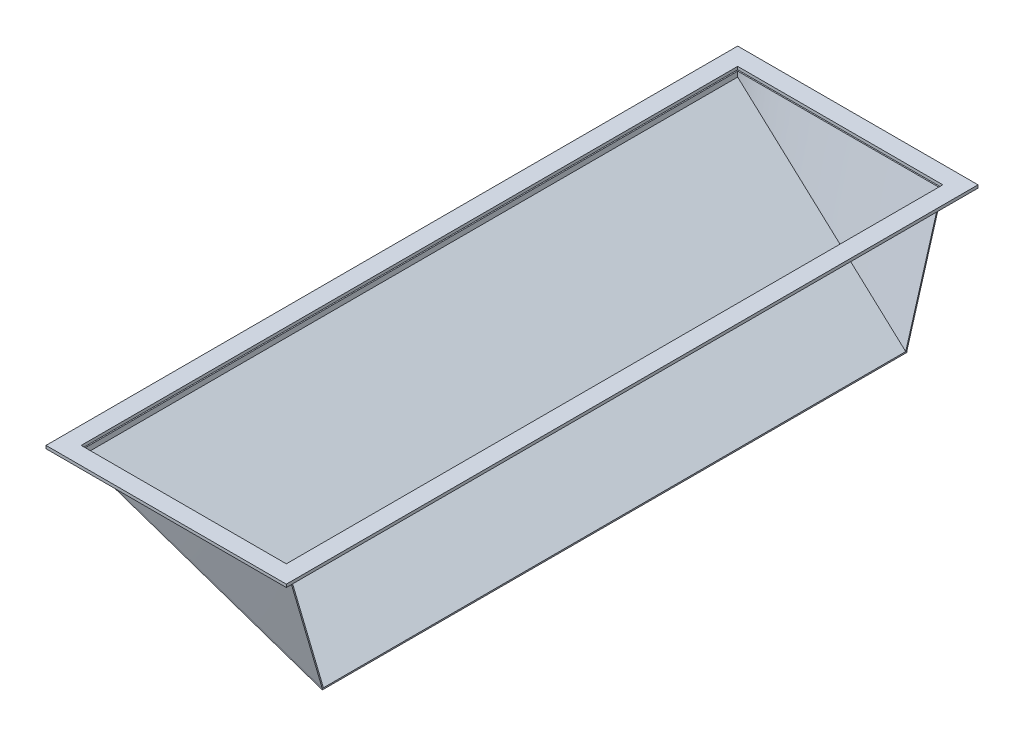
SolidWorks part; units mm, degrees
ref_plane "Płaszczyzna przednia" through (0, 0, 0) normal (0, 0, 1) x (1, 0, 0)
ref_plane "Płaszczyzna górna" through (0, 0, 0) normal (0, 1, 0) x (1, 0, 0)
ref_plane "Płaszczyzna prawa" through (0, 0, 0) normal (1, 0, 0) x (0, 0, -1)
sketch "Szkic1" plane through (0, 0, 0) normal (0, 0, 1) x (1, 0, 0)
  line L0 (0, 0) -> (350, 0)
  line L1 (350, 0) -> (350, -212.0726)
  line L4 (0, 0) -> (0, -10)
  line L6 (0, -10) -> (350, -212.0726)
  dimension "D1" = 350
  dimension "D2" = 10
  dimension "D3" = 120
  dimension "D4" = 0
extrude "Dodanie-wyciągnięcie1" add sketch "Szkic1" along normal blind 1120
sketch "Szkic3" plane through (0, 0, 0) normal (0, 1, 0) x (1, 0, 0)
  line L0 (0, 0) -> (0, -1120)
  line L1 (0, -1120) -> (350, -1120)
  line L2 (350, -1120) -> (350, 0)
  line L3 (350, 0) -> (0, 0)
  line L4 (-30, 30) -> (380, 30)
  line L5 (380, 30) -> (380, -1150)
  line L6 (380, -1150) -> (-30, -1150)
  line L7 (-30, -1150) -> (-30, 30)
  line L8 (0, -1120) -> (0, 0) construction
  line L9 (350, -1120) -> (0, -1120) construction
  line L10 (350, -1120) -> (350, 0) construction
  line L12 (350, 0) -> (0, 0) construction
  dimension "D1" = 30
  dimension "D2" = 30
  dimension "D3" = 30
  dimension "D4" = 30
  dimension "D5" = 0
  dimension "D6" = 0
  dimension "D7" = 0
  dimension "D8" = 0
extrude "Dodanie-wyciągnięcie2" add sketch "Szkic3" along normal blind 5 separate body
shell "Skorupa3" thickness 2
sketch "Szkic5" plane through (-3.3301, -5.7679, 0) normal (0.5, 0.866, 0) x (0.866, -0.5, 0)
  line L2 (6.1547, 0) -> (611.6038, -92.328)
  line L3 (6.1547, -1120) -> (574.3818, -1033.3482)
  line L4 (616.2975, 26.333) -> (611.6038, -92.328)
  line L5 (6.1547, 0) -> (500.0467, 176.7687)
  line L6 (500.0467, 176.7687) -> (616.2975, 26.333)
  line L7 (6.1547, -1120) -> (177.8275, -1478.3965)
  line L8 (177.8275, -1478.3965) -> (567.5714, -1205.5231)
  line L9 (574.3818, -1033.3482) -> (567.5714, -1205.5231)
extrude "Wytnij-wyciągnięcie1" cut sketch "Szkic5" against normal blind 90
sketch "Szkic6" plane through (0, 0, 0) normal (0, -1, 0) x (1, 0, 0)
  line L0 (2, 1120) -> (350, 1120)
  line L1 (350, 1120) -> (350, 1118)
  line L2 (350, 1120) -> (350, 0) construction
  line L3 (350, 1118) -> (2, 1118)
  line L4 (2, 1120) -> (2, 0) construction
  line L5 (2, 1118) -> (2, 1120)
  dimension "D1" = 2
sketch "Szkic7" plane through (-3.3301, -5.7679, 0) normal (0.5, 0.866, 0) x (0.866, -0.5, 0)
  line L0 (6.1547, -1120) -> (407.9905, -1058.722)
  line L1 (6.1547, -1120) -> (6.1547, -1118)
  line L2 (6.1547, -1120) -> (6.1547, 0) construction
  line L3 (6.1547, -1118) -> (407.9905, -1056.6989)
  line L4 (407.9905, -1058.722) -> (407.9905, -1056.6989)
  dimension "D1" = 2
loft "Wyciągnięcie po profilach2" add profiles "Szkic7", "Szkic6"
ref_plane "Płaszczyzna1" through (0, 0, 560) normal (0, 0, -1) x (-1, 0, 0)
mirror "Lustro1" about plane through (0, 0, 560) normal (0, 0, -1) of bodies 105
